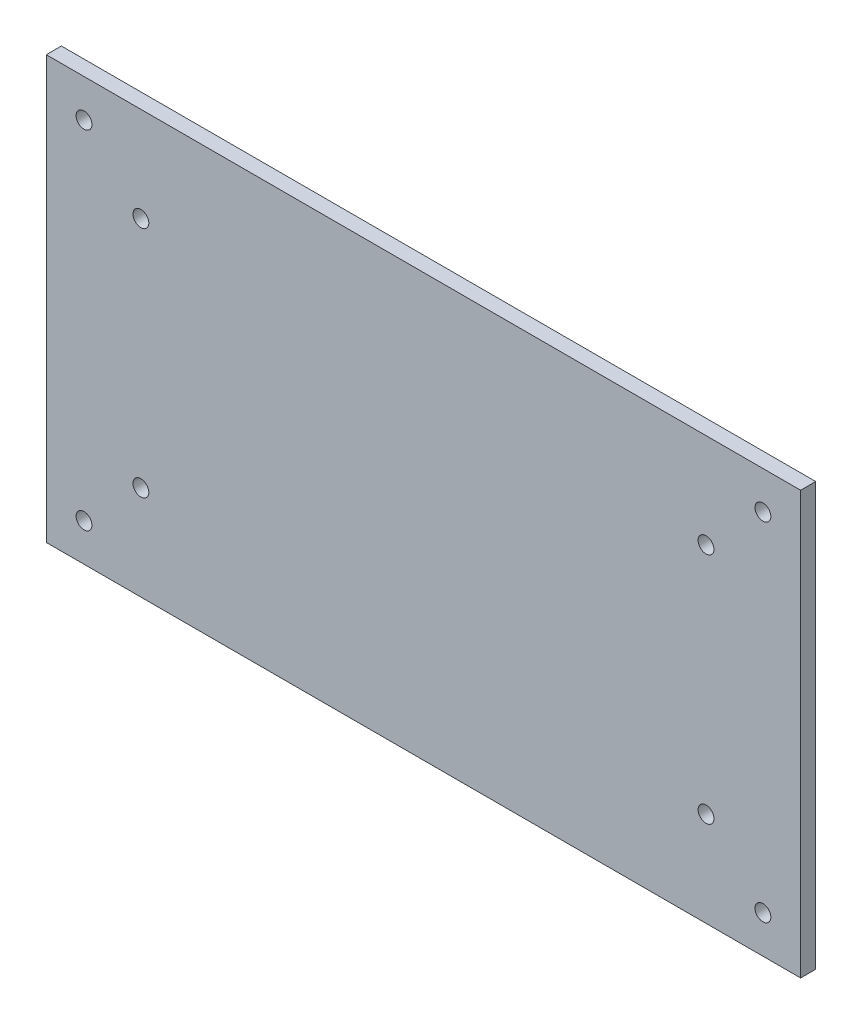
SolidWorks part; units mm, degrees
ref_plane "Plan de face" through (0, 0, 0) normal (0, 0, 1) x (1, 0, 0)
ref_plane "Plan de dessus" through (0, 0, 0) normal (0, 1, 0) x (1, 0, 0)
ref_plane "Plan de droite" through (0, 0, 0) normal (1, 0, 0) x (0, 0, -1)
sketch "Esquisse1" plane through (0, 0, 0) normal (0, 0, 1) x (1, 0, 0)
  line L0 (-50.4043, 162.9474) -> (-50.4043, 126.9474) construction
  line L1 (-10.4043, 162.9474) -> (-90.4043, 162.9474) construction
  line L2 (-10.4043, 162.9474) -> (-10.4043, 126.9474) construction
  line L3 (-10.4043, 126.9474) -> (-90.4043, 126.9474) construction
  line L4 (-90.4043, 162.9474) -> (-90.4043, 126.9474) construction
  line L5 (-90.4043, 144.9474) -> (-10.4043, 144.9474) construction
  line L6 (-64.8369, 204.9474) -> (-64.8369, -145.0526) construction
  line L8 (-100.4043, 172.9474) -> (-0.4043, 172.9474)
  line L9 (-100.4043, 172.9474) -> (-100.4043, 116.9474)
  line L10 (-100.4043, 116.9474) -> (-0.4043, 116.9474)
  line L11 (-0.4043, 172.9474) -> (-0.4043, 116.9474)
  line L12 (-100.4043, 172.9474) -> (-0.4043, 116.9474) construction
  line L13 (-100.4043, 116.9474) -> (-0.4043, 172.9474) construction
  circle A0 centre (-5.4043, 167.9474) radius 1.05
  circle A1 centre (-95.4043, 167.9474) radius 1.05
  circle A2 centre (-95.4043, 121.9474) radius 1.05
  circle A3 centre (-5.4043, 121.9474) radius 1.05
  circle A4 centre (-12.9443, 129.4874) radius 1.05
  circle A5 centre (-12.9443, 160.4074) radius 1.05
  circle A6 centre (-87.8643, 129.4874) radius 1.05
  circle A7 centre (-87.8643, 160.4074) radius 1.05
  point P16 (-50.4043, 144.9474)
  point P17 (-50.4043, 144.9474)
  dimension "D3" = 2.1
  dimension "D8" = 2.54
  dimension "D1" = 80
  dimension "D2" = 36
  dimension "D4" = 5
  dimension "D5" = 5
  dimension "D6" = 10
  dimension "D7" = 10
  dimension "D9" = 2.54
  dimension "D10" = 90
  dimension "D11" = 46
extrude "Boss.-Extru.1" add sketch "Esquisse1" along normal blind 2
